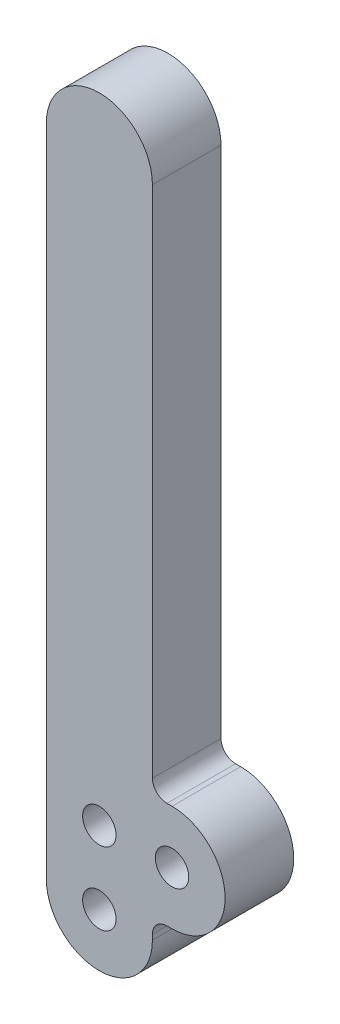
SolidWorks part; units mm, degrees
material "Acrylic (Medium-high impact)"
ref_plane "Front Plane" through (0, 0, 0) normal (0, 0, 1) x (1, 0, 0)
ref_plane "Top Plane" through (0, 0, 0) normal (0, 1, 0) x (1, 0, 0)
ref_plane "Right Plane" through (0, 0, 0) normal (1, 0, 0) x (0, 0, -1)
sketch "Sketch1" plane through (0, 0, 0) normal (0, 0, 1) x (1, 0, 0)
  line L0 (4.6355, 0) -> (4.6355, 0.4445)
  line L1 (5.9055, 1.7145) -> (6.35, 1.7145)
  line L2 (-4.6355, 0) -> (-4.6355, 57.15)
  line L3 (6.35, 10.9855) -> (5.9055, 10.9855)
  line L4 (4.6355, 12.2555) -> (4.6355, 57.15)
  circle A0 centre (0, 0) radius 1.4605
  circle A1 centre (0, 6.35) radius 1.4605
  circle A2 centre (6.35, 6.35) radius 1.4605
  arc A3 (-4.6355, 0) -> (4.6355, 0) centre (0, 0) ccw
  arc A4 (6.35, 1.7145) -> (6.35, 10.9855) centre (6.35, 6.35) ccw
  arc A5 (4.6355, 57.15) -> (-4.6355, 57.15) centre (0, 57.15) ccw
  arc A6 (4.6355, 0.4445) -> (5.9055, 1.7145) centre (5.9055, 0.4445) cw
  arc A7 (4.6355, 12.2555) -> (5.9055, 10.9855) centre (5.9055, 12.2555) ccw
  dimension "D2" = 2.921
  dimension "D4" = 1.27
  dimension "D5" = 1.27
  dimension "D6" = 3.175
  dimension "D1" = 6.35
  dimension "D3" = 6.35
  dimension "D7" = 57.15
extrude "Boss-Extrude1" add sketch "Sketch1" along normal blind 5.9944
